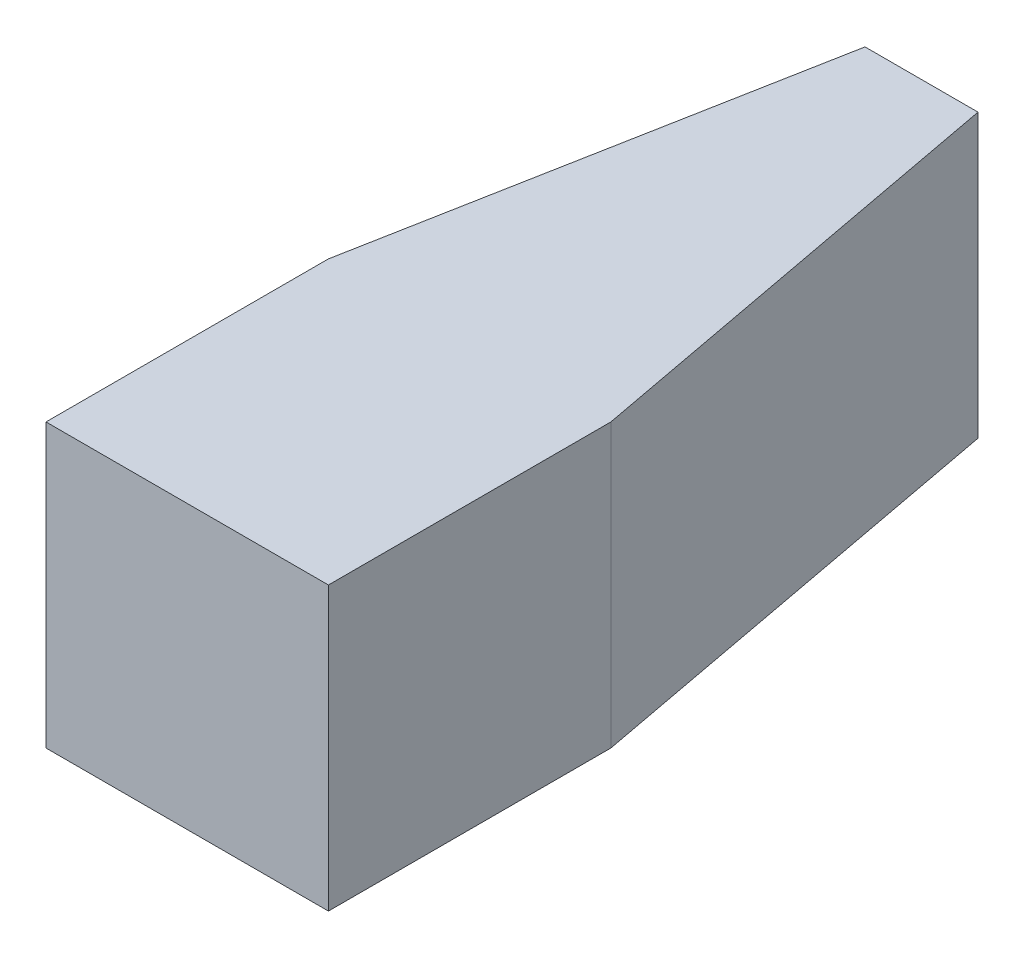
SolidWorks part; units mm, degrees
ref_plane "Front Plane" through (0, 0, 0) normal (0, 0, 1) x (1, 0, 0)
ref_plane "Top Plane" through (0, 0, 0) normal (0, 1, 0) x (1, 0, 0)
ref_plane "Right Plane" through (0, 0, 0) normal (1, 0, 0) x (0, 0, -1)
sketch "Sketch1" plane through (0, 0, 0) normal (0, 1, 0) x (1, 0, 0)
  line L0 (-3.175, 0) -> (0, 0)
  line L1 (0, 0) -> (0, 3.175)
  line L2 (0, 3.175) -> (-0.9525, 8.255)
  line L3 (-0.9525, 8.255) -> (-2.2225, 8.255)
  line L4 (-2.2225, 8.255) -> (-3.175, 3.175)
  line L5 (-3.175, 3.175) -> (-3.175, 0)
  dimension "D1" = 3.175
  dimension "D2" = 3.175
  dimension "D3" = 8.255
  dimension "D4" = 1.27
extrude "Boss-Extrude1" add sketch "Sketch1" along normal blind 3.175
